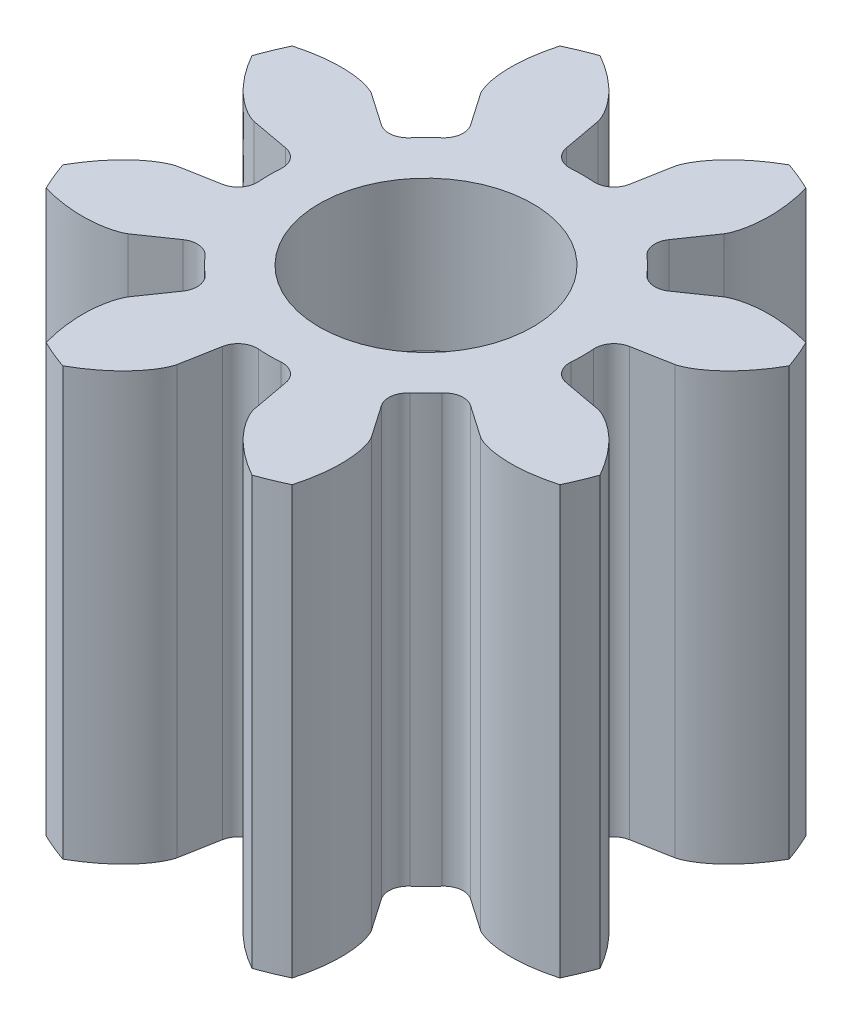
SolidWorks part; units mm, degrees
ref_plane "Front Plane" through (0, 0, 0) normal (0, 0, 1) x (1, 0, 0)
ref_plane "Top Plane" through (0, 0, 0) normal (0, 1, 0) x (1, 0, 0)
ref_plane "Right Plane" through (0, 0, 0) normal (1, 0, 0) x (0, 0, -1)
sketch "Sketch1" plane through (0, 0, 0) normal (0, 1, 0) x (1, 0, 0)
  circle A0 centre (0, 0) radius 6.6667
  dimension "D1" = 13.3333
extrude "Boss-Extrude1" add sketch "Sketch1" along normal blind 10
sketch "Sketch2" plane through (0, 0, 0) normal (0, -1, 0) x (1, 0, 0)
  line L0 (0, 0) -> (3.6065, 0.6617) construction
  line L1 (3.6065, 0.6617) -> (4.9294, 0.9044)
  line L2 (0, 0) -> (3.6065, -0.6617) construction
  line L3 (3.6065, -0.6617) -> (4.9294, -0.9044)
  circle A0 centre (0, 0) radius 3.6667 construction
  circle A1 centre (0, 0) radius 5.3333 construction
  circle A2 centre (0, 0) radius 5.0117 construction
  arc A3 (3.6065, -0.6617) -> (3.6065, 0.6617) centre (0, 0) ccw
  circle A4 centre (0, 0) radius 6.6667
  circle A5 centre (0, 0) radius 6.6667 construction
  arc A6 (6.2882, -2.2143) -> (6.2882, 2.2143) centre (0, 0) ccw
  spline S0 degree 4 poles (4.9294, 0.9044) (4.9322, 0.9049) (4.94, 0.9067) (4.9546, 0.9106) (4.9782, 0.9179) (5.0216, 0.9334) (5.0726, 0.9551) (5.129, 0.9826) (5.1884, 1.015) (5.2383, 1.0446) (5.2873, 1.0757) (5.3354, 1.1082) (5.3927, 1.1493) (5.46, 1.201) (5.5367, 1.2647) (5.6211, 1.3409) (5.7042, 1.4226) (5.7836, 1.5063) (5.8609, 1.5945) (5.9337, 1.6825) (6.0061, 1.7774) (6.0713, 1.8668) (6.1408, 1.9708) (6.1959, 2.0558) (6.2645, 2.1718) (6.3038, 2.2414) (6.3484, 2.3242) (6.3674, 2.3616) (6.3792, 2.3846) knots 0 0 0 0 0 0.005377 0.015084 0.028532 0.04661 0.092111 0.119476 0.146842 0.174209 0.201575 0.228941 0.256307 0.307035 0.361767 0.4165 0.471232 0.525964 0.580697 0.635429 0.690161 0.744894 0.799626 0.854358 0.909091 0.954545 1 1 1 1 1 construction
  spline S1 degree 4 poles (4.9294, 0.9044) (4.9322, 0.9049) (4.94, 0.9067) (4.9546, 0.9106) (4.9782, 0.9179) (5.0216, 0.9334) (5.0726, 0.9551) (5.129, 0.9826) (5.1884, 1.015) (5.2383, 1.0446) (5.2873, 1.0757) (5.3354, 1.1082) (5.3927, 1.1493) (5.46, 1.201) (5.5367, 1.2647) (5.6211, 1.3409) (5.7042, 1.4226) (5.7836, 1.5063) (5.8609, 1.5945) (5.9337, 1.6825) (6.0061, 1.7774) (6.0713, 1.8668) (6.1408, 1.9708) (6.1959, 2.0558) (6.2496, 2.1466) (6.2753, 2.1913) (6.2882, 2.2143) knots 0 0 0 0 0 0.005377 0.015084 0.028532 0.04661 0.092111 0.119476 0.146842 0.174209 0.201575 0.228941 0.256307 0.307035 0.361767 0.4165 0.471232 0.525964 0.580697 0.635429 0.690161 0.744894 0.799626 0.854358 0.909091 0.909091 0.909091 0.909091 0.909091
  spline S2 degree 4 poles (4.9294, -0.9044) (4.9322, -0.9049) (4.94, -0.9067) (4.9546, -0.9106) (4.9782, -0.9179) (5.0216, -0.9334) (5.0726, -0.9551) (5.129, -0.9826) (5.1884, -1.015) (5.2383, -1.0446) (5.2873, -1.0757) (5.3354, -1.1082) (5.3927, -1.1493) (5.46, -1.201) (5.5367, -1.2647) (5.6211, -1.3409) (5.7042, -1.4226) (5.7836, -1.5063) (5.8609, -1.5945) (5.9337, -1.6825) (6.0061, -1.7774) (6.0713, -1.8668) (6.1408, -1.9708) (6.1959, -2.0558) (6.2645, -2.1718) (6.3038, -2.2414) (6.3484, -2.3242) (6.3674, -2.3616) (6.3792, -2.3846) knots 0 0 0 0 0 0.005377 0.015084 0.028532 0.04661 0.092111 0.119476 0.146842 0.174209 0.201575 0.228941 0.256307 0.307035 0.361767 0.4165 0.471232 0.525964 0.580697 0.635429 0.690161 0.744894 0.799626 0.854358 0.909091 0.954545 1 1 1 1 1 construction
  spline S3 degree 4 poles (4.9294, -0.9044) (4.9322, -0.9049) (4.94, -0.9067) (4.9546, -0.9106) (4.9782, -0.9179) (5.0216, -0.9334) (5.0726, -0.9551) (5.129, -0.9826) (5.1884, -1.015) (5.2383, -1.0446) (5.2873, -1.0757) (5.3354, -1.1082) (5.3927, -1.1493) (5.46, -1.201) (5.5367, -1.2647) (5.6211, -1.3409) (5.7042, -1.4226) (5.7836, -1.5063) (5.8609, -1.5945) (5.9337, -1.6825) (6.0061, -1.7774) (6.0713, -1.8668) (6.1408, -1.9708) (6.1959, -2.0558) (6.2496, -2.1466) (6.2753, -2.1913) (6.2882, -2.2143) knots 0 0 0 0 0 0.005377 0.015084 0.028532 0.04661 0.092111 0.119476 0.146842 0.174209 0.201575 0.228941 0.256307 0.307035 0.361767 0.4165 0.471232 0.525964 0.580697 0.635429 0.690161 0.744894 0.799626 0.854358 0.909091 0.909091 0.909091 0.909091 0.909091
  circle M9 centre (0, 0) radius 6.6667
  dimension "D2" = 7.3333
  dimension "D3" = 10.6667
  dimension "D4" = 10.0234
extrude "Cut-Extrude1" cut sketch "Sketch2" against normal through all contours L3 S3 S1 L1 A3 M9
fillet "Fillet1" radius 0.4473 2 edges at (3.6065, 5, -0.6617) (3.6065, 5, 0.6617)
pattern_circular "CirPattern1" count 8 every 45 about axis through (0, 10, 0) along (0, -1, 0) of "Cut-Extrude1", "Fillet1"
sketch "Sketch3" plane through (0, 0, 0) normal (0, -1, 0) x (1, 0, 0)
  circle A0 centre (0, 0) radius 2.5
  dimension "D1" = 5
extrude "Cut-Extrude2" cut sketch "Sketch3" against normal blind 3.5
sketch "Sketch4" plane through (0, 10, 0) normal (0, 1, 0) x (1, 0, 0)
  circle A0 centre (0, 0) radius 2.5
  dimension "D1" = 5
extrude "Cut-Extrude3" cut sketch "Sketch4" against normal offset from surface (3.5 mm away) 3 up to face at (0, 3.5, -2.5)
sketch "Sketch5" plane through (0, 6.5, 0) normal (0, 1, 0) x (1, 0, 0)
  circle A0 centre (0, 0) radius 1.1
  dimension "D1" = 2.2
extrude "Cut-Extrude4" cut sketch "Sketch5" against normal through all
sketch "Sketch6" plane through (0, 0, 0) normal (0, -1, 0) x (1, 0, 0)
  line L0 (0, 0) -> (0, 2.5) construction
  line L1 (-0.2, 2.492) -> (0, 2.4)
  line L2 (0, 2.4) -> (0.2, 2.492)
  line L3 (-0.2, 2.492) -> (0.2, 2.492) construction
  circle A0 centre (0, 0) radius 2.5 construction
  circle A1 centre (0, 0) radius 2.5 construction
  arc A2 (-0.2, 2.492) -> (0.2, 2.492) centre (0, 0) cw
  dimension "D1" = 0.4
  dimension "D2" = 0.1
extrude "Boss-Extrude2" add sketch "Sketch6" against normal up to next (3.5 mm away) contours A2 L1 L2
pattern_circular "CirPattern2" count 36 every 10 about axis through (0, 0, 0) along (0, 1, 0) of "Boss-Extrude2"
equation "\"DiametralPitch\"= 0.75"
equation "\"NumTeeth\"= 8"
equation "\"PressureAngle\"= 20deg"
equation "\"Addendum\"= 1 / \"DiametralPitch\""
equation "\"Dedendum\"= 1.25 / \"DiametralPitch\""
equation "\"WorkingDepth\"= 2 / \"DiametralPitch\""
equation "\"WholeDepth\"= 2.25 / \"DiametralPitch\""
equation "\"Clearance\"= 0.25 / \"DiametralPitch\""
equation "\"ToothThickness\"= 1.5708 / \"DiametralPitch\""
equation "\"CircularPitch\"= pi / \"DiametralPitch\""
equation "\"PitchCircle\"= \"NumTeeth\" / \"DiametralPitch\""
equation "\"OutsideDiameter\"= ( \"NumTeeth\" + 2 ) / \"DiametralPitch\""
equation "\"Fillet\"= \"Clearance\" * cos ( \"PressureAngle\" ) * tan ( ( 90 + \"PressureAngle\" ) / 2 )"
equation "\"AddendumCircle\"= \"PitchCircle\" + ( 2 * \"Addendum\" )"
equation "\"DedendumCircle\"= \"PitchCircle\" - ( 2 * \"Dedendum\" )"
equation "\"BaseCircle\"= \"PitchCircle\" * cos ( \"PressureAngle\" )"
equation "\"PitchAngle\"= 360deg / \"NumTeeth\""
equation "\"Alpha\"= sqr ( \"PitchCircle\" ^ 2 - \"BaseCircle\" ^ 2 ) / \"BaseCircle\" * 180 / PI - \"PressureAngle\""
equation "\"Beta\"= ( \"PitchAngle\" / 4 - \"Alpha\" )"
equation "\"Phi\"= sqr ( ( \"AddendumCircle\" / 2 ) ^ 2 - ( \"BaseCircle\" / 2 ) ^ 2 ) / ( \"BaseCircle\" / 2 )"
equation "\"D1@Sketch1\"=\"OutsideDiameter\""
equation "\"D2@Sketch2\"=\"DedendumCircle\""
equation "\"D3@Sketch2\"=\"PitchCircle\""
equation "\"D4@Sketch2\"=\"BaseCircle\""
equation "\"D1@Fillet1\"=\"Fillet\""
equation "\"D2@CirPattern1\"=\"PitchAngle\""
equation "\"D1@CirPattern1\"=\"NumTeeth\""
